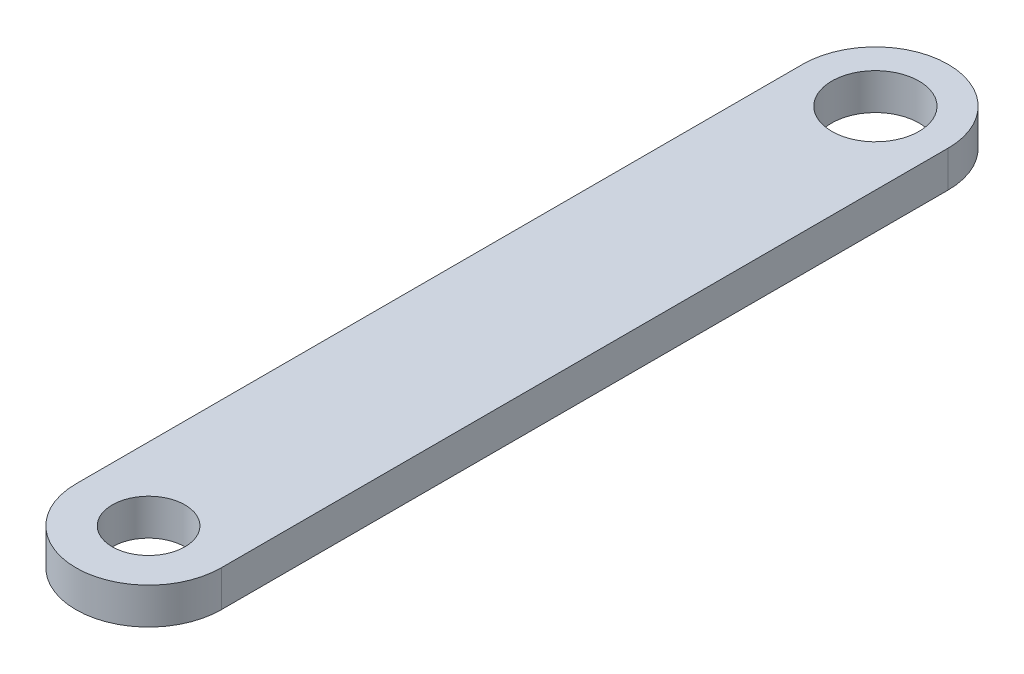
SolidWorks part; units mm, degrees
material "1060 Alloy"
ref_plane "Front Plane" through (0, 0, 0) normal (0, 0, 1) x (1, 0, 0)
ref_plane "Top Plane" through (0, 0, 0) normal (0, 1, 0) x (1, 0, 0)
ref_plane "Right Plane" through (0, 0, 0) normal (1, 0, 0) x (0, 0, -1)
sketch "Sketch1" plane through (0, 0, 0) normal (0, 1, 0) x (1, 0, 0)
  line L0 (0, 0) -> (0, -100) construction
  line L1 (10, 0) -> (10, -100)
  line L2 (-10, 0) -> (-10, -100)
  circle A0 centre (0, 0) radius 6
  circle A1 centre (0, -100) radius 5
  arc A2 (10, 0) -> (-10, 0) centre (0, 0) ccw
  arc A3 (-10, -100) -> (10, -100) centre (0, -100) ccw
  point P5 (0, -50)
  dimension "D1" = 12
  dimension "D2" = 10
  dimension "D4" = 10
  dimension "D3" = 100
extrude "Boss-Extrude1" add sketch "Sketch1" along normal blind 5
